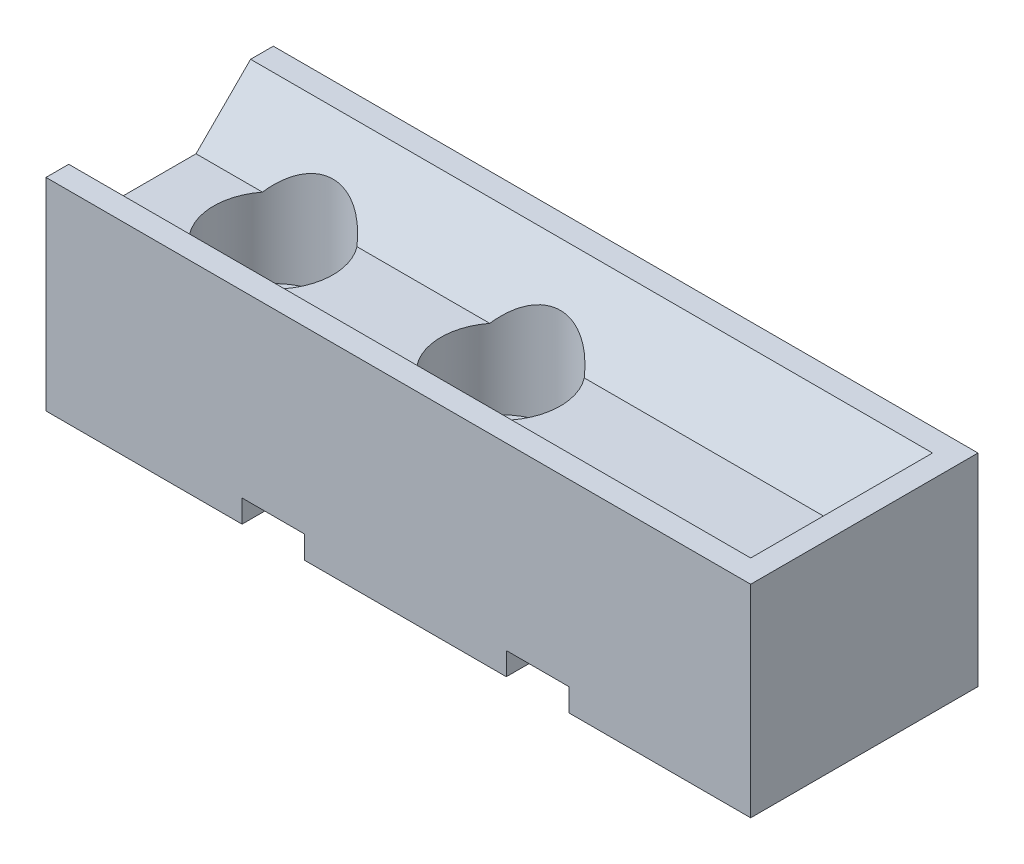
SolidWorks part; units mm, degrees
ref_plane "Front Plane" through (0, 0, 0) normal (0, 0, 1) x (1, 0, 0)
ref_plane "Top Plane" through (0, 0, 0) normal (0, 1, 0) x (1, 0, 0)
ref_plane "Right Plane" through (0, 0, 0) normal (1, 0, 0) x (0, 0, -1)
sketch "Sketch1" plane through (0, 0, 0) normal (0, 1, 0) x (1, 0, 0)
  line L1 (-31, -10) -> (31, -10)
  line L2 (-31, -10) -> (-31, 10)
  line L3 (-31, 10) -> (31, 10)
  line L4 (31, -10) -> (31, 10)
  line L5 (-31, -10) -> (31, 10) construction
  line L6 (-31, 10) -> (31, -10) construction
  point P0 (0, 0)
  dimension "D1" = 62
  dimension "D2" = 20
extrude "Boss-Extrude1" add sketch "Sketch1" along normal blind 13
sketch "Sketch2" plane through (-31, 0, 0) normal (-1, 0, 0) x (0, 0, 1)
  line L0 (3.2, 13) -> (8, 17.8)
  line L1 (-10, 13) -> (10, 13) construction
  line L2 (8, 17.8) -> (10, 17.8)
  line L3 (10, 17.8) -> (10, 13)
  line L4 (10, 13) -> (3.2, 13)
  line L5 (10, 13) -> (10, 0) construction
  line L6 (0, 0) -> (0, 13) construction
  line L7 (-10, 13) -> (-3.2, 13)
  line L8 (-10, 17.8) -> (-10, 13)
  line L9 (-8, 17.8) -> (-10, 17.8)
  line L10 (-3.2, 13) -> (-8, 17.8)
  dimension "D1" = 2
  dimension "D2" = 45
  dimension "D3" = 3.2
extrude "Boss-Extrude2" add sketch "Sketch2" against normal up to surface (62 mm away) up to face at (31, 6.5, 0)
sketch "Sketch3" plane through (0, 13, 0) normal (0, 1, 0) x (1, 0, 0)
  line L0 (31, 10) -> (-31, 10) construction
  line L1 (31, -10) -> (29, -10)
  line L2 (31, -10) -> (31, 10)
  line L3 (31, 10) -> (29, 10)
  line L4 (29, -10) -> (29, 10)
  dimension "D1" = 2
extrude "Boss-Extrude3" add sketch "Sketch3" along normal up to surface (4.8 mm away) up to face at (0, 17.8, -9)
sketch "Sketch6" plane through (0, 13, 0) normal (0, 1, 0) x (1, 0, 0)
  line L0 (-31, 3.2) -> (-31, -3.2) construction
  circle A0 centre (-21, 0) radius 2.75
  circle A1 centre (-1, 0) radius 2.75
  point P0 (-31, 0)
  dimension "D1" = 5.5
  dimension "D2" = 10
  dimension "D3" = 20
extrude "Cut-Extrude1" cut sketch "Sketch6" against normal through all
sketch "Sketch7" plane through (0, 0, 0) normal (0, 1, 0) x (1, 0, 0)
  line L0 (0, 0) -> (0, 10) construction
  line L1 (31, 10) -> (-31, 10) construction
  circle A0 centre (-21, 0) radius 5.25
  circle A1 centre (-1, 0) radius 5.25
  dimension "D1" = 10.5
extrude "Cut-Extrude2" cut sketch "Sketch7" along normal through all from offset 6
sketch "Sketch8" plane through (0, 0, -10) normal (0, 0, -1) x (-1, 0, 0)
  line L0 (-31, 0) -> (31, 0) construction
  line L1 (-15, 0) -> (-9.5, 0)
  line L2 (-15, 0) -> (-15, 2)
  line L3 (-15, 2) -> (-9.5, 2)
  line L4 (-9.5, 0) -> (-9.5, 2)
  line L5 (-31, 17.8) -> (-31, 0) construction
  line L6 (11, 2) -> (11, 0) construction
  line L7 (13.75, 0) -> (8.25, 0)
  line L8 (13.75, 0) -> (13.75, 2)
  line L9 (13.75, 2) -> (8.25, 2)
  line L10 (8.25, 0) -> (8.25, 2)
  line L11 (31, 17.8) -> (31, 0) construction
  dimension "D1" = 2
  dimension "D2" = 5.5
  dimension "D3" = 16
  dimension "D4" = 20
extrude "Cut-Extrude3" cut sketch "Sketch8" against normal through all
